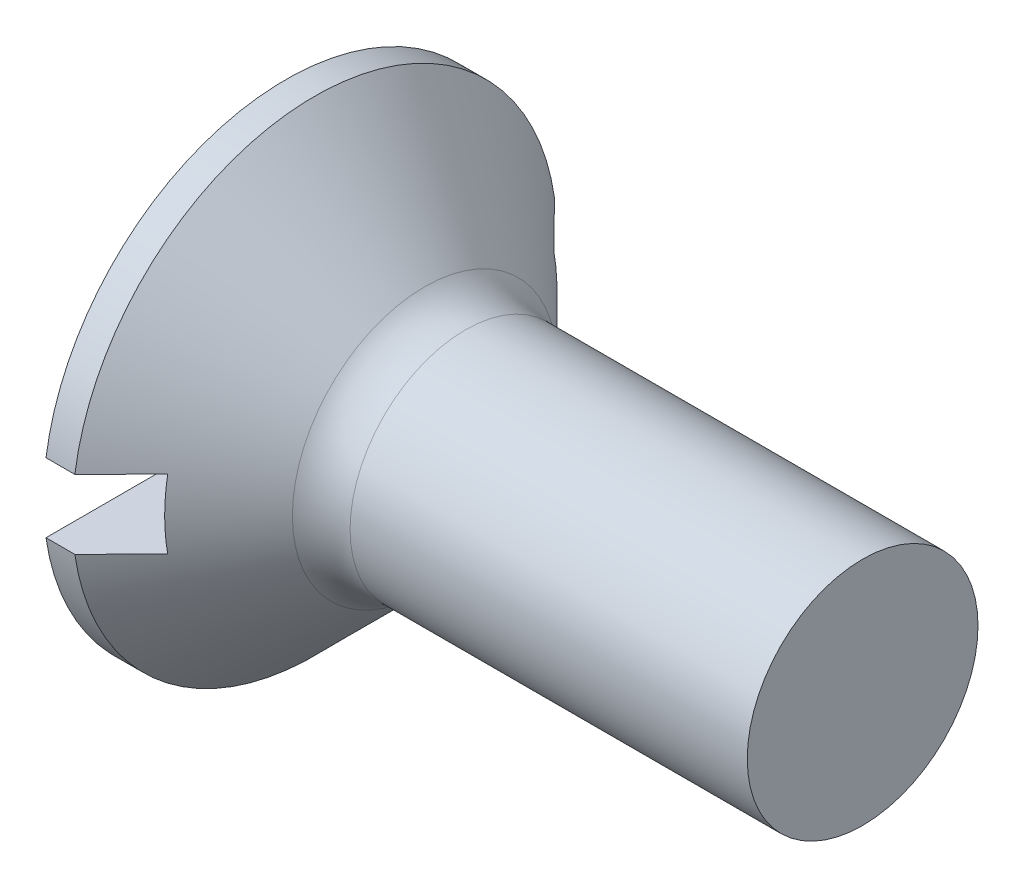
SolidWorks part; units mm, degrees
ref_plane "Plane1" through (0, 0, 0) normal (0, 0, 1) x (1, 0, 0)
ref_plane "Plane2" through (0, 0, 0) normal (0, 1, 0) x (1, 0, 0)
ref_plane "Plane3" through (0, 0, 0) normal (1, 0, 0) x (0, 0, -1)
revolve "Base-Revolve" add sketch "BodySke" angle 360 about L5
sketch "BodySke" plane through (0, 0, 0) normal (0, 0, 1) x (1, 0, 0)
  line L0 (0, 0) -> (0, 4.2)
  line L1 (0, 4.2) -> (0.5, 4.2)
  line L2 (2.7, 2) -> (10, 2)
  line L3 (10, 2) -> (10, 0)
  line L4 (10, 0) -> (0, 0)
  line L5 (-6.35, 0) -> (82.55, 0) construction
  line L6 (2.7, -2) -> (10, -2) construction
  line L7 (0.5, -4.2) -> (2.7, -2) construction
  line L8 (0.5, 4.2) -> (2.7, 2)
  line L9 (0, -4.2) -> (0.5, -4.2) construction
  line L10 (3.4, 3.5875) -> (3.4, -5.9375) construction
  line L11 (0, 6.35) -> (0, -3.175) construction
  dimension "Diameter" = 4
  dimension "Length" = 10
  dimension "Head_ht" = 2.7
  dimension "Head_dia" = 8.4
  dimension "Head_ang" = 90
  dimension "D6" = 0.5
  dimension "Advance" = 0.7
  dimension "Thread_nom" = 10
cosmetic thread "ThreadCosmetic" parameters "Thread_length"=6.6, "Thread_minor"=3.22
extrude "Slot" cut sketch "Sketch2" against normal blind 1.3
sketch "Sketch2" plane through (0, 0, 0) normal (-1, 0, 0) x (0, 0, 1)
  line L0 (-4.2, -0.6) -> (4.2, -0.6)
  line L1 (-4.2, -0.6) -> (-4.2, 0.6)
  line L2 (4.2, 0.6) -> (-4.2, 0.6)
  line L3 (4.2, 0.6) -> (4.2, -0.6)
  dimension "D1" = 0.6
  dimension "Slot_width" = 1.2
  dimension "D2" = 8.4
  dimension "D3" = 4.2
fillet "Fillet1" radius 1 1 edges at (2.7, 0, 2)
sketch "ThdSchSke" plane through (0, 0, 0) normal (0, 0, 1) x (1, 0, 0)
  line L0 (3.4, -1.61) -> (3.1269, -2)
  line L1 (3.4, -1.61) -> (3.6731, -2)
  line L2 (3.6731, -2) -> (3.6731, -2.5)
  line L3 (-3.175, 0) -> (5.1513, 0) construction
  line L5 (3.6731, -2.5) -> (3.1269, -2.5)
  line L6 (3.1269, -2.5) -> (3.1269, -2)
  line L7 (0, 4.2) -> (0, 0.6) construction
  dimension "Thread_minor" = 3.22
  dimension "Diameter" = 4
  dimension "Start" = 3.4
  dimension "SideAngle" = 55
  dimension "VeeAngle" = 70
  dimension "Overcut" = 5
revolve "ThreadSchematic" cut sketch "ThdSchSke" angle 360 about L3
pattern_linear "ThdSchPat"
equation "\"D1@Sketch2\" = \"Slot_width@Sketch2\" / 2"
equation "\"D2@Sketch2\" = \"Head_dia@BodySke\""
equation "\"D3@Sketch2\" = \"D2@Sketch2\" / 2"
equation "\"Thread_length@ThreadCosmetic\" = ((sgn( (\"Length@BodySke\" - \"Advance@BodySke\" * 1.0 - \"Head_ht@BodySke\" ) - \"Thread_nom@BodySke\" )-1)*( (\"Length@BodySke\" - \"Advance@BodySke\" * 1.0 - \"Head_ht@BodySke\" ) - \"Thread_nom@BodySke\" ))/-2+ \"Thread_nom@BodySke\""
equation "\"Thread_minor@ThdSchSke\" = \"Thread_minor@ThreadCosmetic\""
equation "\"Diameter@ThdSchSke\" = \"Diameter@BodySke\""
equation "\"Overcut@ThdSchSke\" = \"Diameter@BodySke\" * 1.25"
equation "\"Start@ThdSchSke\" = 0.000001 + \"Length@BodySke\" - \"Thread_length@ThreadCosmetic\"  '---Countersunk---"
equation "\"Num_threads@ThdSchPat\" = int( \"Thread_length@ThreadCosmetic\" / \"Advance@BodySke\" + 0.999 )  + 1"
equation "\"Advance@ThdSchPat\" = \"Thread_length@ThreadCosmetic\" /  (\"Num_threads@ThdSchPat\" - 1) 'relax it"
